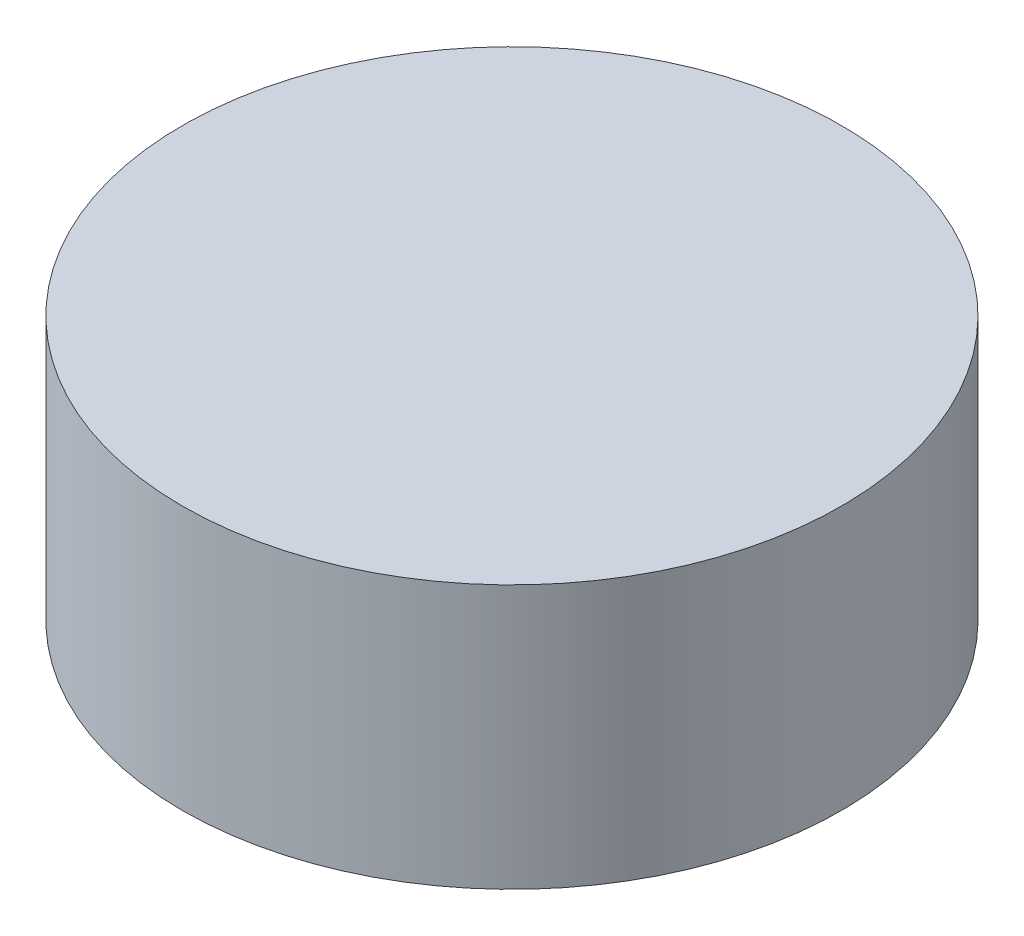
SolidWorks part; units mm, degrees
ref_plane "Front Plane" through (0, 0, 0) normal (0, 0, 1) x (1, 0, 0)
ref_plane "Top Plane" through (0, 0, 0) normal (0, 1, 0) x (1, 0, 0)
ref_plane "Right Plane" through (0, 0, 0) normal (1, 0, 0) x (0, 0, -1)
sketch "Sketch2" plane through (0, 0, 0) normal (0, 1, 0) x (1, 0, 0)
  circle A0 centre (0, 0) radius 32.5
extrude "Boss-Extrude1" add sketch "Sketch2" along normal blind 26
sketch "Sketch3" plane through (0, 0, 0) normal (0, -1, 0) x (1, 0, 0)
  circle A0 centre (0, 0) radius 4
extrude "Boss-Extrude2" add sketch "Sketch3" along normal blind 4.5
